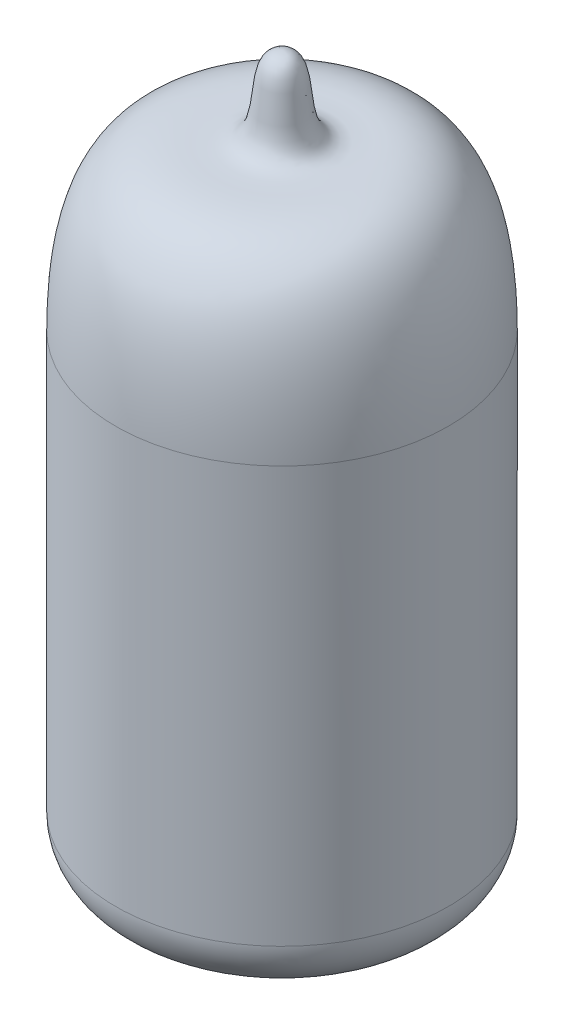
SolidWorks part; units mm, degrees
material "Glass"
ref_plane "Front Plane" through (0, 0, 0) normal (0, 0, 1) x (1, 0, 0)
ref_plane "Top Plane" through (0, 0, 0) normal (0, 1, 0) x (1, 0, 0)
ref_plane "Right Plane" through (0, 0, 0) normal (1, 0, 0) x (0, 0, -1)
sketch "Sketch1" plane through (0, 0, 0) normal (0, 0, 1) x (1, 0, 0)
  line L0 (0, 0) -> (0, 47) construction
  line L1 (0, 0) -> (7.5, 0)
  line L2 (11, 3.5) -> (11, 31)
  line L3 (10.7, 5.8864) -> (10.7, 31)
  line L4 (0, 2.6864) -> (0, 0.3)
  line L5 (0, 47) -> (0, 46.7)
  line L6 (0, 0.3) -> (0, 0)
  line L7 (0, 2.6864) -> (7.5, 2.6864)
  line L9 (10.7, 3.5) -> (10.7, 31) construction
  line L10 (0, 0.3) -> (7.5, 0.3) construction
  arc A0 (7.5, 0) -> (11, 3.5) centre (7.5, 3.5) ccw
  arc A2 (7.5, 2.6864) -> (10.7, 5.8864) centre (7.5, 5.8864) ccw
  arc A3 (7.5, 0.3) -> (10.7, 3.5) centre (7.5, 3.5) ccw construction
  spline S0 degree 3 poles (0, 47) (1.8685, 47) (0.84, 43.098) (3.6908, 40.9093) (11, 43.7319) (11, 31) knots 0 0 0 0 0.457353 0.557353 1 1 1 1
  spline S1 degree 1 poles (0, 46.7) (10.7, 31) knots 0 0 1 1 construction
  spline S2 degree 3 poles (0, 46.7) (0.0898, 46.7) (0.2867, 46.6754) (0.5268, 46.5614) (0.8624, 46.1825) (1.0447, 45.2079) (1.1533, 44.0769) (1.2796, 43.2249) (1.5261, 42.4404) (2.0047, 41.7697) (2.8936, 41.4236) (4.0869, 41.4554) (5.4939, 41.4636) (6.9642, 41.1863) (8.1238, 40.4977) (8.9656, 39.5147) (9.5355, 38.5143) (10.0209, 37.2077) (10.3973, 35.5591) (10.6004, 33.8592) (10.6852, 32.3089) (10.7, 31.4275) (10.7, 31) knots 0 0 0 0 0.03125 0.0625 0.125 0.25 0.3125 0.375 0.4375 0.5 0.5625 0.625 0.6875 0.75 0.8125 0.84375 0.875 0.90625 0.9375 0.96875 0.984375 1 1 1 1
  dimension "D4" = 3.5
  dimension "D1" = 47
  dimension "D2" = 11
  dimension "D3" = 16
  dimension "D5" = 0.3
revolve "Revolve1" add sketch "Sketch1" angle 360 about L0
